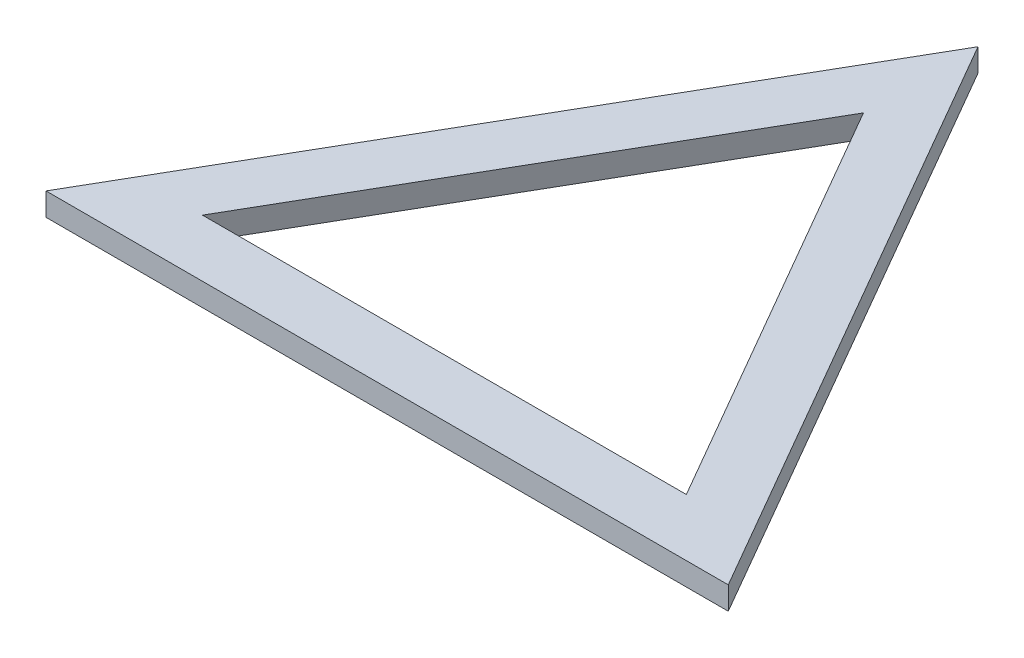
SolidWorks part; units mm, degrees
ref_plane "Front Plane" through (0, 0, 0) normal (0, 0, 1) x (1, 0, 0)
ref_plane "Top Plane" through (0, 0, 0) normal (0, 1, 0) x (1, 0, 0)
ref_plane "Right Plane" through (0, 0, 0) normal (1, 0, 0) x (0, 0, -1)
sketch "Sketch1" plane through (0, 0, 0) normal (0, 1, 0) x (1, 0, 0)
  line L0 (0, 0) -> (29.8074, 51.6279)
  line L1 (29.8074, 51.6279) -> (59.6148, 0)
  line L2 (59.6148, 0) -> (0, 0)
  line L3 (50.9474, 5.0041) -> (8.6674, 5.0041)
  line L4 (8.6674, 5.0041) -> (29.8074, 41.6197)
  line L5 (29.8074, 41.6197) -> (50.9474, 5.0041)
  dimension "D1" = 42.28
  dimension "D2" = 59.6148
extrude "Boss-Extrude1" add sketch "Sketch1" along normal blind 2 contours L3 L4 L5 | L2 L0 L1
equation "\"innerlen\"=32.9559"
equation "\"inner\"=42.28"
equation "\"D1@Sketch1\"=\"inner\""
equation "\"D2@Sketch1\"=1.41*\"inner\""
